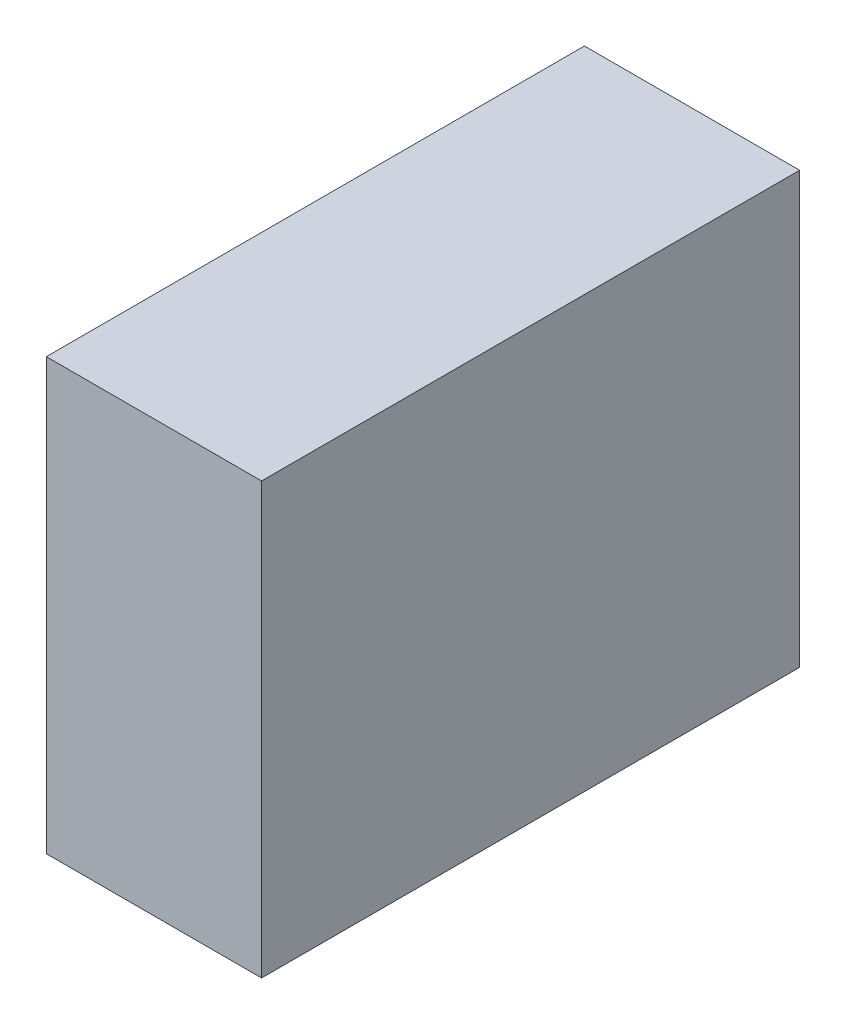
SolidWorks part; units mm, degrees
ref_plane "Front Plane" through (0, 0, 0) normal (0, 0, 1) x (1, 0, 0)
ref_plane "Top Plane" through (0, 0, 0) normal (0, 1, 0) x (1, 0, 0)
ref_plane "Right Plane" through (0, 0, 0) normal (1, 0, 0) x (0, 0, -1)
sketch "Sketch1" plane through (0, 0, 0) normal (0, 0, 1) x (1, 0, 0)
  line L1 (0, 0) -> (20, 0)
  line L2 (0, 0) -> (0, -40)
  line L3 (0, -40) -> (20, -40)
  line L4 (20, 0) -> (20, -40)
  dimension "D1" = 20
  dimension "D2" = 40
extrude "Extrude1" add sketch "Sketch1" along normal blind 50
